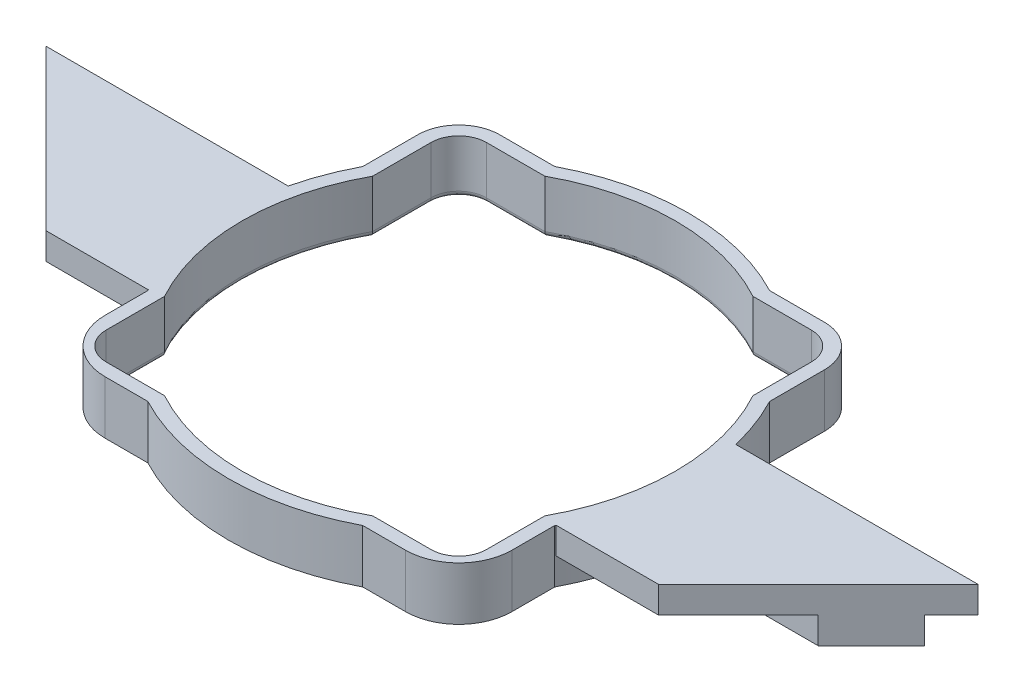
SolidWorks part; units mm, degrees
ref_plane "Front Plane" through (0, 0, 0) normal (0, 0, 1) x (1, 0, 0)
ref_plane "Top Plane" through (0, 0, 0) normal (0, 1, 0) x (1, 0, 0)
ref_plane "Right Plane" through (0, 0, 0) normal (1, 0, 0) x (0, 0, -1)
sketch "Sketch1" plane through (0, 0, 0) normal (0, 1, 0) x (1, 0, 0)
  line L1 (-127, -76.2) -> (127, -76.2)
  line L2 (-127, -76.2) -> (-127, 76.2)
  line L3 (-127, 76.2) -> (127, 76.2)
  line L4 (127, -76.2) -> (127, 76.2)
  line L5 (-127, -76.2) -> (127, 76.2) construction
  line L6 (-127, 76.2) -> (127, -76.2) construction
  point P0 (0, 0)
  dimension "D1" = 254
  dimension "D2" = 152.4
extrude "Boss-Extrude1" add sketch "Sketch1" along normal blind 12.7 contours L2 L3 L4 L1
sketch "Sketch4" plane through (0, 0, 0) normal (0, -1, 0) x (1, 0, 0)
  line L0 (45.339, 24.8219) -> (45.339, 38.735)
  line L1 (38.735, 45.339) -> (24.8219, 45.339)
  line L2 (-24.8219, 45.339) -> (-38.735, 45.339)
  line L3 (-45.339, 38.735) -> (-45.339, 24.8219)
  line L4 (-45.339, -24.8219) -> (-45.339, -38.735)
  line L5 (-38.735, -45.339) -> (-24.8219, -45.339)
  line L6 (24.8219, -45.339) -> (38.735, -45.339)
  line L7 (45.339, -38.735) -> (45.339, -24.8219)
  line L9 (45.085, 24.7569) -> (45.085, 38.735)
  line L10 (38.735, 45.085) -> (24.7569, 45.085)
  line L11 (-24.7569, 45.085) -> (-38.735, 45.085)
  line L12 (-45.085, 38.735) -> (-45.085, 24.7569)
  line L13 (-45.085, -24.7569) -> (-45.085, -38.735)
  line L14 (-38.735, -45.085) -> (-24.7569, -45.085)
  line L15 (24.7569, -45.085) -> (38.735, -45.085)
  line L24 (45.085, -38.735) -> (45.085, -24.7569)
  line L25 (45.085, 24.7569) -> (45.085, 38.735) construction
  line L26 (38.735, 45.085) -> (24.7569, 45.085) construction
  line L27 (-24.7569, 45.085) -> (-38.735, 45.085) construction
  line L28 (-45.085, 38.735) -> (-45.085, 24.7569) construction
  line L29 (-45.085, -24.7569) -> (-45.085, -38.735) construction
  line L30 (-38.735, -45.085) -> (-24.7569, -45.085) construction
  line L31 (24.7569, -45.085) -> (38.735, -45.085) construction
  line L32 (45.085, -38.735) -> (45.085, -24.7569) construction
  line L33 (48.514, 25.6213) -> (48.514, 38.735)
  line L34 (38.735, 48.514) -> (25.6213, 48.514)
  line L35 (-25.6213, 48.514) -> (-38.735, 48.514)
  line L36 (-48.514, 38.735) -> (-48.514, 25.6213)
  line L37 (-48.514, -25.6213) -> (-48.514, -38.735)
  line L38 (-38.735, -48.514) -> (-25.6213, -48.514)
  line L39 (25.6213, -48.514) -> (38.735, -48.514)
  line L40 (48.514, -38.735) -> (48.514, -25.6213)
  arc A0 (45.339, 38.735) -> (38.735, 45.339) centre (38.735, 38.735) ccw
  arc A1 (24.8219, 45.339) -> (-24.8219, 45.339) centre (0, 0) ccw
  arc A2 (-38.735, 45.339) -> (-45.339, 38.735) centre (-38.735, 38.735) ccw
  arc A3 (-45.339, 24.8219) -> (-45.339, -24.8219) centre (0, 0) ccw
  arc A4 (-45.339, -38.735) -> (-38.735, -45.339) centre (-38.735, -38.735) ccw
  arc A5 (-24.8219, -45.339) -> (24.8219, -45.339) centre (0, 0) ccw
  arc A6 (38.735, -45.339) -> (45.339, -38.735) centre (38.735, -38.735) ccw
  arc A7 (45.339, -24.8219) -> (45.339, 24.8219) centre (0, 0) ccw
  arc A24 (45.085, 38.735) -> (38.735, 45.085) centre (38.735, 38.735) ccw
  arc A25 (24.7569, 45.085) -> (-24.7569, 45.085) centre (0, 0) ccw
  arc A26 (-38.735, 45.085) -> (-45.085, 38.735) centre (-38.735, 38.735) ccw
  arc A27 (-45.085, 24.7569) -> (-45.085, -24.7569) centre (0, 0) ccw
  arc A28 (-45.085, -38.735) -> (-38.735, -45.085) centre (-38.735, -38.735) ccw
  arc A29 (-24.7569, -45.085) -> (24.7569, -45.085) centre (0, 0) ccw
  arc A30 (38.735, -45.085) -> (45.085, -38.735) centre (38.735, -38.735) ccw
  arc A31 (45.085, -24.7569) -> (45.085, 24.7569) centre (0, 0) ccw
  arc A32 (45.085, 38.735) -> (38.735, 45.085) centre (38.735, 38.735) ccw construction
  arc A33 (24.7569, 45.085) -> (-24.7569, 45.085) centre (0, 0) ccw construction
  arc A34 (-38.735, 45.085) -> (-45.085, 38.735) centre (-38.735, 38.735) ccw construction
  arc A35 (-45.085, 24.7569) -> (-45.085, -24.7569) centre (0, 0) ccw construction
  arc A36 (-45.085, -38.735) -> (-38.735, -45.085) centre (-38.735, -38.735) ccw construction
  arc A37 (-24.7569, -45.085) -> (24.7569, -45.085) centre (0, 0) ccw construction
  arc A38 (38.735, -45.085) -> (45.085, -38.735) centre (38.735, -38.735) ccw construction
  arc A39 (45.085, -24.7569) -> (45.085, 24.7569) centre (0, 0) ccw construction
  arc A40 (48.514, 38.735) -> (38.735, 48.514) centre (38.735, 38.735) ccw
  arc A41 (25.6213, 48.514) -> (-25.6213, 48.514) centre (0, 0) ccw
  arc A42 (-38.735, 48.514) -> (-48.514, 38.735) centre (-38.735, 38.735) ccw
  arc A43 (-48.514, 25.6213) -> (-48.514, -25.6213) centre (0, 0) ccw
  arc A44 (-48.514, -38.735) -> (-38.735, -48.514) centre (-38.735, -38.735) ccw
  arc A45 (-25.6213, -48.514) -> (25.6213, -48.514) centre (0, 0) ccw
  arc A46 (38.735, -48.514) -> (48.514, -38.735) centre (38.735, -38.735) ccw
  arc A47 (48.514, -25.6213) -> (48.514, 25.6213) centre (0, 0) ccw
  dimension "D1" = 0
  dimension "D2" = 0.254
  dimension "D3" = 3.175
extrude "Cut-Extrude1" cut sketch "Sketch4" against normal through all flip side to cut
sketch "Sketch5" plane through (0, 0, 0) normal (0, 1, 0) x (1, 0, 0)
  line L0 (54.4953, 6.35) -> (104.775, 6.35)
  line L1 (104.775, 6.35) -> (92.075, -6.35)
  line L2 (92.075, -6.35) -> (54.4953, -6.35)
  line L3 (0, 0) -> (0, 33.5108) construction
  line L4 (-92.075, -6.35) -> (-54.4953, -6.35)
  line L5 (-104.775, 6.35) -> (-92.075, -6.35)
  line L6 (-54.4953, 6.35) -> (-104.775, 6.35)
  arc A0 (48.514, -25.6213) -> (48.514, 25.6213) centre (0, 0) ccw construction
  arc A1 (54.4953, -6.35) -> (54.4953, 6.35) centre (0, 0) ccw
  arc A2 (-54.4953, -6.35) -> (-54.4953, 6.35) centre (0, 0) cw
  point P9 (98.425, 0)
  dimension "D1" = 12.7
  dimension "D2" = 104.775
  dimension "D3" = 45
extrude "Boss-Extrude2" add sketch "Sketch5" along normal blind 6.35
sketch "Sketch6" plane through (0, 0, 0) normal (0, 1, 0) x (1, 0, 0)
  line L0 (53.3739, 12.7) -> (111.125, 12.7)
  line L1 (111.125, 12.7) -> (73.025, -25.4)
  line L2 (73.025, -25.4) -> (48.6302, -25.4)
  line L3 (92.075, -6.35) -> (104.775, 6.35) construction
  line L4 (104.775, 6.35) -> (54.4953, 6.35) construction
  line L5 (54.4953, -6.35) -> (92.075, -6.35) construction
  line L6 (0, 0) -> (0, 23.3719) construction
  line L7 (-73.025, -25.4) -> (-48.6302, -25.4)
  line L8 (-111.125, 12.7) -> (-73.025, -25.4)
  line L9 (-53.3739, 12.7) -> (-111.125, 12.7)
  arc A0 (48.514, -25.6213) -> (48.514, 25.6213) centre (0, 0) ccw construction
  arc A1 (48.6302, -25.4) -> (53.3739, 12.7) centre (0, 0) ccw
  arc A2 (-48.6302, -25.4) -> (-53.3739, 12.7) centre (0, 0) cw
  dimension "D1" = 6.35
  dimension "D2" = 19.05
extrude "Boss-Extrude3" add sketch "Sketch6" along normal blind 6.35 from surface at 6.35 starting at face at (76.5523, 6.35, 0)
fillet "Fillet1" radius 1.27 16 edges at (45.339, 0, 31.7785) (43.4047, 0, 43.4047) (-31.7785, 0, 45.339) (-43.4047, 0, 43.4047) (-45.339, 0, -31.7785) (-43.4047, 0, -43.4047) (45.339, 0, -31.7785) (43.4047, 0, -43.4047) (51.689, 0, 0) (31.7785, 0, 45.339) (0, 0, 51.689) (-45.339, 0, 31.7785) (-51.689, 0, 0) (-31.7785, 0, -45.339) (0, 0, -51.689) (31.7785, 0, -45.339)
sketch "Sketch9" plane through (0, 12.7, 0) normal (0, 1, 0) x (1, 0, 0)
  line L0 (48.514, -25.6213) -> (48.514, -38.735) construction
  line L1 (38.735, -48.514) -> (25.6213, -48.514) construction
  line L2 (0, 0) -> (0, -39.3727) construction
  line L3 (38.735, -48.514) -> (35.814, -48.514)
  line L4 (48.514, -35.814) -> (48.514, -38.735)
  line L5 (-48.514, -35.814) -> (-48.514, -38.735)
  line L6 (-38.735, -48.514) -> (-35.814, -48.514)
  arc A0 (35.814, -48.514) -> (48.514, -35.814) centre (35.814, -35.814) ccw
  arc A1 (38.735, -48.514) -> (48.514, -38.735) centre (38.735, -38.735) ccw construction
  arc A2 (38.735, -48.514) -> (48.514, -38.735) centre (38.735, -38.735) ccw
  arc A3 (-38.735, -48.514) -> (-48.514, -38.735) centre (-38.735, -38.735) cw
  arc A4 (-35.814, -48.514) -> (-48.514, -35.814) centre (-35.814, -35.814) cw
  dimension "D1" = 25.4
extrude "Cut-Extrude3" cut sketch "Sketch9" against normal through all
equation "\"tightTol\"= 0.005in"
equation "\"normTol\"= 0.01in"
equation "\"looseTol\"= 0.02in"
equation "\"D2@Sketch4\"=\"normTol\""
